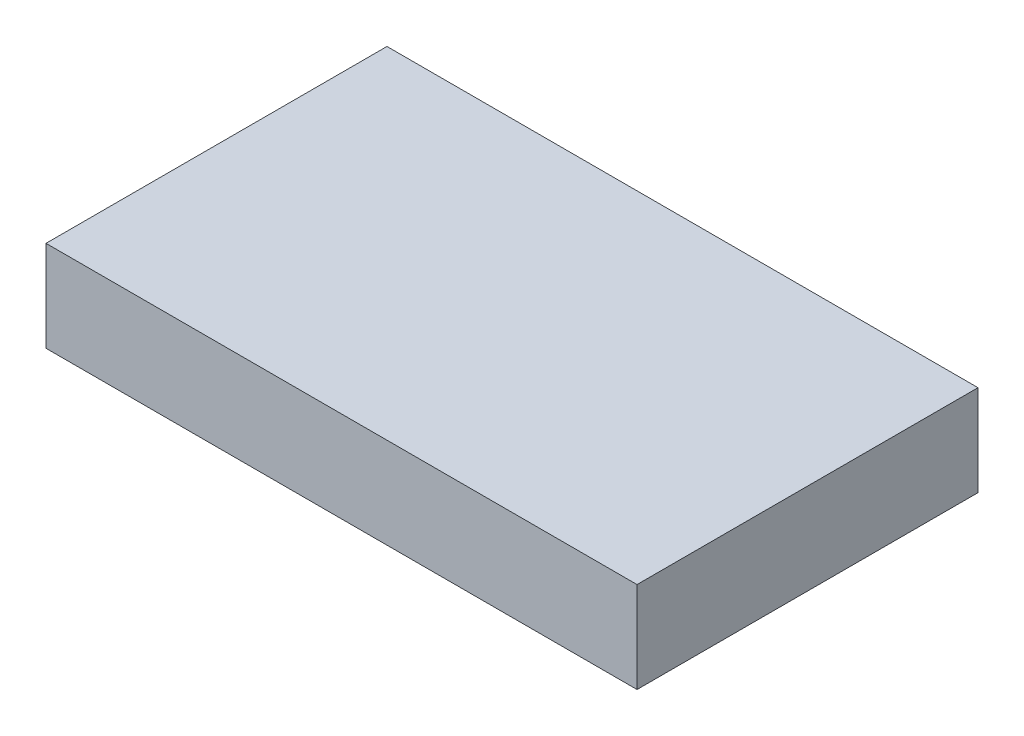
SolidWorks part; units mm, degrees
material "Ceramic Porcelain"
ref_plane "Front Plane" through (0, 0, 0) normal (0, 0, 1) x (1, 0, 0)
ref_plane "Top Plane" through (0, 0, 0) normal (0, 1, 0) x (1, 0, 0)
ref_plane "Right Plane" through (0, 0, 0) normal (1, 0, 0) x (0, 0, -1)
sketch "Sketch1" plane through (0, 0, 0) normal (0, 1, 0) x (1, 0, 0)
  line L1 (-27.549, 19.8127) -> (24.451, 19.8127)
  line L2 (-27.549, 19.8127) -> (-27.549, -10.1873)
  line L3 (-27.549, -10.1873) -> (24.451, -10.1873)
  line L4 (24.451, 19.8127) -> (24.451, -10.1873)
  dimension "D1" = 52
  dimension "D2" = 30
extrude "Boss-Extrude1" add sketch "Sketch1" along normal blind 8
ref_plane "Plane1" through (-1.549, 0, 0) normal (1, 0, 0) x (0, 0, -1)
